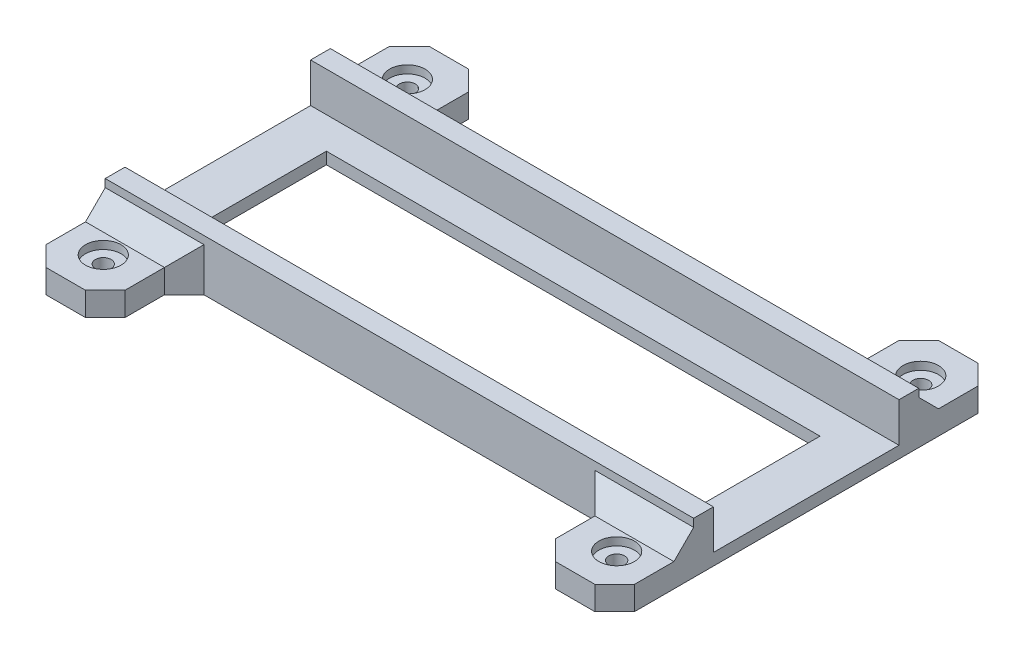
SolidWorks part; units mm, degrees
ref_plane "Front Plane" through (0, 0, 0) normal (0, 0, 1) x (1, 0, 0)
ref_plane "Top Plane" through (0, 0, 0) normal (0, 1, 0) x (1, 0, 0)
ref_plane "Right Plane" through (0, 0, 0) normal (1, 0, 0) x (0, 0, -1)
sketch "Sketch1" plane through (0, 0, 0) normal (0, 1, 0) x (1, 0, 0)
  line L0 (-74.5, 28.5) -> (74.5, 28.5)
  line L1 (-74.5, 23.5) -> (74.5, 23.5)
  line L2 (-69.5, 23.5) -> (-69.5, -23.5)
  line L3 (-74.5, -23.5) -> (74.5, -23.5)
  line L4 (69.5, 23.5) -> (69.5, -23.5)
  line L5 (-69.5, 23.5) -> (69.5, -23.5) construction
  line L6 (-69.5, -23.5) -> (69.5, 23.5) construction
  line L7 (74.5, 28.5) -> (74.5, -28.5)
  line L8 (-74.5, -28.5) -> (74.5, -28.5)
  line L9 (-74.5, 28.5) -> (-74.5, -28.5)
  line L10 (-69.5, 23.5) -> (69.5, 23.5) construction
  line L11 (-69.5, -23.5) -> (69.5, -23.5) construction
  point P0 (0, 0)
  dimension "D1" = 139
  dimension "D2" = 47
  dimension "D3" = 5
extrude "Boss-Extrude1" add sketch "Sketch1" along normal blind 10 contours L0 L9 L1 L7 | L3 L9 L8 L7
sketch "Sketch2" plane through (0, 0, 0) normal (0, -1, 0) x (1, 0, 0)
  line L1 (74.5, 28.5) -> (-74.5, 28.5)
  line L2 (74.5, 28.5) -> (74.5, -28.5)
  line L3 (74.5, -28.5) -> (-74.5, -28.5)
  line L4 (-74.5, 28.5) -> (-74.5, -28.5)
extrude "Boss-Extrude2" add sketch "Sketch2" along normal blind 3
sketch "Sketch3" plane through (0, 0, 0) normal (0, 1, 0) x (1, 0, 0)
  line L0 (-74.5, 23.5) -> (74.5, 23.5) construction
  line L1 (-62.5, -15.5) -> (62.5, -15.5)
  line L2 (-62.5, -15.5) -> (-62.5, 15.5)
  line L3 (-62.5, 15.5) -> (62.5, 15.5)
  line L4 (62.5, -15.5) -> (62.5, 15.5)
  line L5 (-62.5, -15.5) -> (62.5, 15.5) construction
  line L6 (-62.5, 15.5) -> (62.5, -15.5) construction
  point P0 (0, 0)
  dimension "D1" = 125
  dimension "D2" = 8
extrude "Cut-Extrude1" cut sketch "Sketch3" against normal blind 20
sketch "Sketch4" plane through (0, 0, 0) normal (0, 1, 0) x (1, 0, 0)
  line L1 (-74.5, 28.5) -> (-54.5, 28.5)
  line L2 (-74.5, 28.5) -> (-74.5, 48.5)
  line L3 (-74.5, 48.5) -> (-54.5, 48.5)
  line L4 (-54.5, 28.5) -> (-54.5, 48.5)
  dimension "D1" = 20
  dimension "D2" = 20
extrude "Boss-Extrude3" add sketch "Sketch4" against normal up to surface (3 mm away) and the other way blind 3 up to face at (0, -3, 0)
sketch "Sketch5" plane through (0, 3, 0) normal (0, 1, 0) x (1, 0, 0)
  line L0 (-74.5, 48.5) -> (-74.5, 28.5) construction
  circle A0 centre (-65, 38.5) radius 2
  dimension "D1" = 4
  dimension "D2" = 9.5
extrude "Cut-Extrude2" cut sketch "Sketch5" against normal blind 20
sketch "Sketch6" plane through (0, 3, 0) normal (0, 1, 0) x (1, 0, 0)
  circle A0 centre (-65, 38.5) radius 4.5
  dimension "D1" = 9
extrude "Cut-Extrude3" cut sketch "Sketch6" against normal blind 2
mirror "Mirror5" about plane through (0, 0, 0) normal (0, 0, 1) of "Boss-Extrude3", "Cut-Extrude3", "Cut-Extrude2" second plane through (0, 0, 0) second plane normal (1, 0, 0)
chamfer "Chamfer1" distance 5 angle 45 16 edges at (74.5, 0, 48.5) (54.5, 0, 28.5) (54.5, 0, 48.5) (64.5, 3, 28.5) (-74.5, 0, -48.5) (-54.5, 0, -28.5) (-54.5, 0, -48.5) (-64.5, 3, -28.5) (74.5, 0, -48.5) (54.5, 0, -48.5) (54.5, 0, -28.5) (64.5, 3, -28.5) (-74.5, 0, 48.5) (-54.5, 0, 48.5) (-54.5, 0, 28.5) (-64.5, 3, 28.5)
